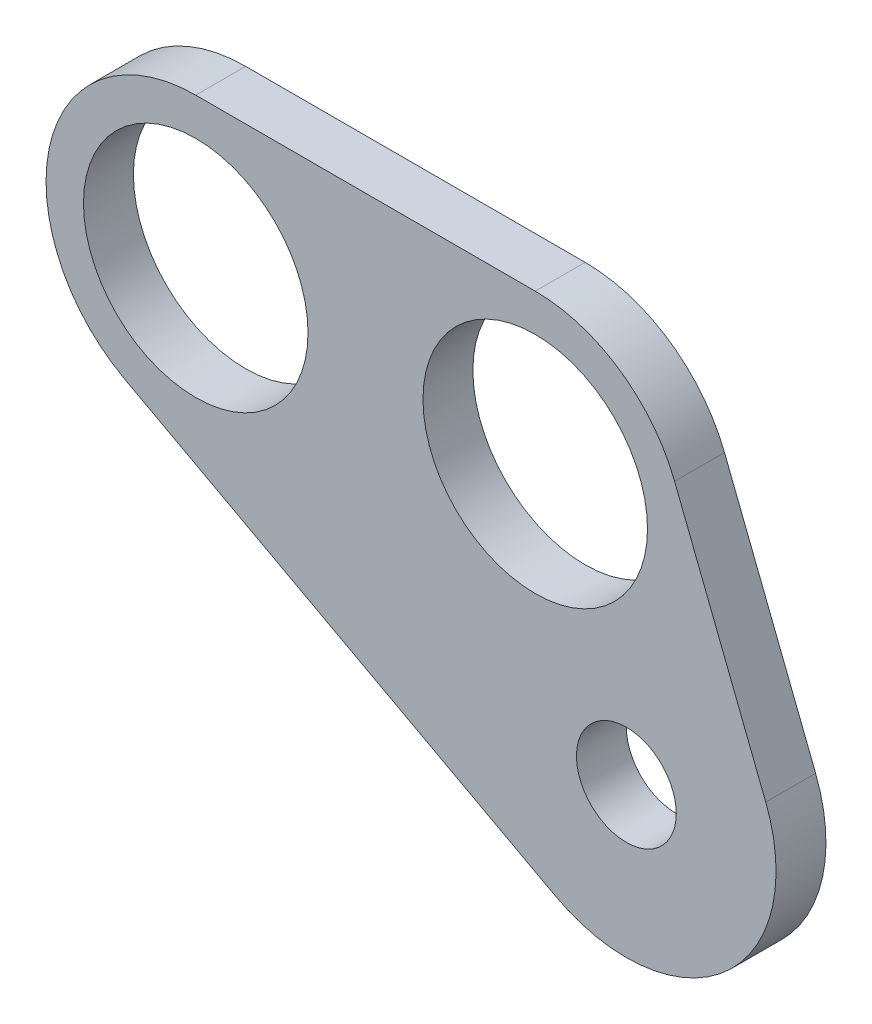
SolidWorks part; units mm, degrees
ref_plane "Front Plane" through (0, 0, 0) normal (0, 0, 1) x (1, 0, 0)
ref_plane "Top Plane" through (0, 0, 0) normal (0, 1, 0) x (1, 0, 0)
ref_plane "Right Plane" through (0, 0, 0) normal (1, 0, 0) x (0, 0, -1)
sketch "Sketch1" plane through (0, 0, 0) normal (0, 0, 1) x (1, 0, 0)
  line L0 (-54.8026, 48.6062) -> (-11.5972, 48.6062)
  line L1 (6.1365, 36.5145) -> (17.7337, 6.9583)
  line L2 (-9.0428, -16.767) -> (-63.8454, 12.7892)
  arc A0 (17.7337, 6.9583) -> (-9.0428, -16.767) centre (0, 0) cw
  arc A1 (-11.5972, 48.6062) -> (6.1365, 36.5145) centre (-11.5972, 29.5562) cw
  arc A2 (-54.8026, 48.6062) -> (-63.8454, 12.7892) centre (-54.8026, 29.5562) ccw
  point P2 (-8.0793, -17.2519)
  point P10 (-130.2567, 48.6062)
  point P12 (0, 0)
  point P13 (0, 0)
  dimension "D1" = 19.05
  dimension "D2" = 43.2054
  dimension "D3" = 62.2647
  dimension "D4" = 31.75
extrude "Boss-Extrude1" add sketch "Sketch1" along normal blind 6.35
hole_wizard "1 (1) Diameter Hole1" positions "Sketch2" profile "Sketch3" hole size "1" standard "ANSI Inch"
sketch "Sketch2" plane through (0, 0, 6.35) normal (0, 0, 1) x (1, 0, 0)
  arc A0 (-54.8026, 48.6062) -> (-63.8454, 12.7892) centre (-54.8026, 29.5562) ccw construction
  arc A1 (6.1365, 36.5145) -> (-11.5972, 48.6062) centre (-11.5972, 29.5562) ccw construction
  point P0 (-54.8026, 29.5562)
  point P2 (-11.5972, 29.5562)
  point P5 (0, 0)
  point P9 (0, 0)
sketch "Sketch3" plane through (-54.8026, 29.5562, 6.35) normal (1, 0, 0) x (0, -1, 0)
  line L0 (0, 0) -> (0, 33.9848)
  line L1 (0, 33.9848) -> (14.2875, 25.4)
  line L2 (14.2875, 25.4) -> (14.2875, 0)
  line L5 (14.2875, 0) -> (0, 0)
  line L10 (0, 33.9848) -> (-14.2875, 25.4) construction
  line L11 (0, -6.35) -> (0, 107.95) construction
  dimension "Hole Dia." = 28.575
  dimension "Hole Depth" = 25.4
  dimension "Drill Angle" = 118
hole_wizard "1/2 (0.5) Diameter Hole1" positions "Sketch4" profile "Sketch5" hole size "1/2" standard "ANSI Inch"
sketch "Sketch4" plane through (0, 0, 6.35) normal (0, 0, 1) x (1, 0, 0)
  point P0 (0, 0)
sketch "Sketch5" plane through (0, 0, 6.35) normal (1, 0, 0) x (0, -1, 0)
  line L0 (0, 0) -> (0, 29.2155)
  line L1 (0, 29.2155) -> (6.35, 25.4)
  line L2 (6.35, 25.4) -> (6.35, 0)
  line L5 (6.35, 0) -> (0, 0)
  line L10 (0, 29.2155) -> (-6.35, 25.4) construction
  line L11 (0, -6.35) -> (0, 107.95) construction
  dimension "Hole Dia." = 12.7
  dimension "Hole Depth" = 25.4
  dimension "Drill Angle" = 118
